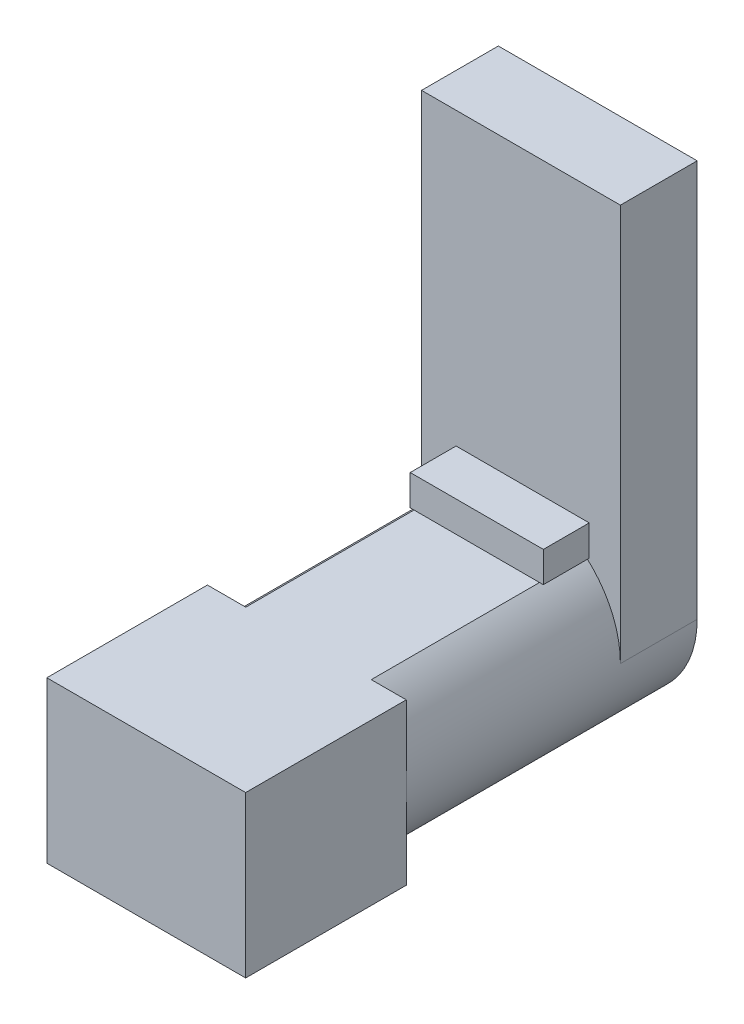
SolidWorks part; units mm, degrees
ref_plane "Front Plane" through (0, 0, 0) normal (0, 0, 1) x (1, 0, 0)
ref_plane "Top Plane" through (0, 0, 0) normal (0, 1, 0) x (1, 0, 0)
ref_plane "Right Plane" through (0, 0, 0) normal (1, 0, 0) x (0, 0, -1)
sketch "Sketch2" plane through (0, 0, 0) normal (0, 0, 1) x (1, 0, 0)
  line L1 (-6.25, -5.3) -> (6.25, -5.3)
  line L2 (-6.25, -5.3) -> (-6.25, 5.3)
  line L3 (-6.25, 5.3) -> (6.25, 5.3)
  line L4 (6.25, -5.3) -> (6.25, 5.3)
  line L5 (-6.25, -5.3) -> (6.25, 5.3) construction
  line L6 (-6.25, 5.3) -> (6.25, -5.3) construction
  line L7 (-6.5, -5.55) -> (6.5, -5.55)
  line L8 (-6.5, -5.55) -> (-6.5, 5.55)
  line L9 (-6.5, 5.55) -> (6.5, 5.55)
  line L10 (6.5, -5.55) -> (6.5, 5.55)
  line L11 (-6.5, -5.55) -> (6.5, 5.55) construction
  line L12 (-6.5, 5.55) -> (6.5, -5.55) construction
  point P0 (0, 0)
  point P6 (0, 0)
  dimension "D1" = 12.5
  dimension "D2" = 10.6
  dimension "D3" = 0.25
  dimension "D4" = 0.25
extrude "Boss-Extrude1" add sketch "Sketch2" along normal blind 10 contours L2 L1 L4 L3 | L8 L7 L10 L9
sketch "Sketch3" plane through (0, 0, 0) normal (0, 0, -1) x (-1, 0, 0)
  line L1 (-6.25, 5.3) -> (6.25, 5.3)
  line L2 (-6.25, 5.3) -> (-6.25, -5.3)
  line L3 (-6.25, -5.3) -> (6.25, -5.3)
  line L4 (6.25, 5.3) -> (6.25, -5.3)
  line L5 (-6.25, 5.3) -> (6.25, -5.3) construction
  line L6 (-6.25, -5.3) -> (6.25, 5.3) construction
  point P0 (0, 0)
extrude "Boss-Extrude2" add sketch "Sketch3" against normal blind 10
sketch "Sketch4" plane through (0, 0, 0) normal (0, 0, -1) x (-1, 0, 0)
  line L0 (-3.3834, -5.55) -> (2.9839, -5.55)
  line L1 (-6.5, 0) -> (6.5, 0) construction
  line L2 (-3.3834, 5.55) -> (2.9839, 5.55)
  line L3 (6.5, 5.55) -> (-6.5, 5.55) construction
  line L4 (-6.5, -5.55) -> (-6.5, 5.55) construction
  line L5 (6.5, -5.55) -> (6.5, 5.55) construction
  arc A0 (-3.3834, -5.55) -> (-3.3834, 5.55) centre (0, 0) cw
  arc A1 (2.9839, -5.55) -> (2.9839, 5.55) centre (0.3617, 0) ccw
  point P15 (-6.5, 0)
  dimension "D1" = 6.1383
extrude "Boss-Extrude3" add sketch "Sketch4" along normal blind 15.5
sketch "Sketch5" plane through (0, 0, -15.5) normal (0, 0, -1) x (-1, 0, 0)
  line L0 (-6.5, 10.96) -> (6.5, 10.96)
  line L1 (-6.5, 10.96) -> (-6.5, 0)
  line L2 (-6.5, 0) -> (6.5, 0)
  line L3 (6.5, 10.96) -> (6.5, 0)
  line L4 (-6.5, 0) -> (-6.5, 5.55) construction
  line L5 (-3.3834, -5.55) -> (2.9839, -5.55)
  arc A0 (-6.5, 0) -> (-3.3834, -5.55) centre (0, 0) ccw
  arc A1 (2.9839, -5.55) -> (6.5, 0) centre (0.3617, 0) ccw
  arc M5 (-3.3834, 5.55) -> (-3.3834, -5.55) centre (0, 0) ccw
  line M6 (-3.3834, -5.55) -> (2.9839, -5.55)
  arc M7 (2.9839, -5.55) -> (2.9839, 5.55) centre (0.3617, 0) ccw
  line M8 (2.9839, 5.55) -> (-3.3834, 5.55)
  dimension "D1" = 10.96
extrude "Boss-Extrude4" add sketch "Sketch5" against normal blind 1.5 contours L2 M5 M6 M7 | L3 L0 L1 M5 M8 M7
sketch "Sketch6" plane through (0, 0, -15.5) normal (0, 0, -1) x (-1, 0, 0)
  line L0 (-6.5, -5.55) -> (-6.5, 0) construction
  line L1 (-6.5, 0) -> (-6.5, 10.96)
  line L2 (-6.5, 10.96) -> (6.5, 10.96)
  line L3 (6.5, 10.96) -> (6.5, 0)
  line L4 (-3.3834, -5.55) -> (2.9839, -5.55)
  arc A0 (-3.3834, -5.55) -> (-6.5, 0) centre (0, 0) cw
  arc A1 (-6.5, 0) -> (-3.3834, -5.55) centre (0, 0) ccw construction
  arc A2 (6.5, 0) -> (2.9839, -5.55) centre (0.3617, 0) cw
extrude "Boss-Extrude5" add sketch "Sketch6" along normal blind 3.52
sketch "Sketch8" plane through (0, 0, -19.02) normal (0, 0, -1) x (-1, 0, 0)
  line L0 (-6.5, 0) -> (6.5, 0) construction
sketch "Sketch9" plane through (0, 0, 10) normal (0, 0, 1) x (1, 0, 0)
  line L1 (-6.5, 5.55) -> (6.5, 5.55)
  line L2 (-6.5, 5.55) -> (-6.5, -5.55)
  line L3 (-6.5, -5.55) -> (6.5, -5.55)
  line L4 (6.5, 5.55) -> (6.5, -5.55)
extrude "Boss-Extrude7" add sketch "Sketch9" along normal blind 0.5
sketch "Sketch10" plane through (-6.5, 0, 0) normal (-1, 0, 0) x (0, 0, 1)
  line L0 (-14, 0) -> (-14, 5.55) construction
  line L1 (10.5, 5.55) -> (-14, 5.55)
  line L2 (10.5, 5.55) -> (10.5, 4.95)
  line L3 (10.5, 4.95) -> (-14, 4.95)
  line L4 (-14, 5.55) -> (-14, 4.95)
  dimension "D1" = 0.6
extrude "Cut-Extrude1" cut sketch "Sketch10" against normal blind 15
sketch "Sketch11" plane through (0, 0, -14) normal (0, 0, 1) x (1, 0, 0)
  line L0 (4.2128, 4.95) -> (-3.9916, 4.95) construction
  line L1 (4.4628, 4.95) -> (-4.2416, 4.95)
  line L2 (0.1106, 4.95) -> (0.1106, 6.95)
  line L3 (4.4628, 6.95) -> (-4.2416, 6.95)
  line L4 (-4.2416, 4.95) -> (-4.2416, 6.95)
  line L5 (4.4628, 4.95) -> (4.4628, 6.95)
  line M6 (-3.9916, 4.95) -> (4.2128, 4.95)
  dimension "D1" = 0.25
  dimension "D2" = 2
extrude "Boss-Extrude8" add sketch "Sketch11" along normal blind 3 contours L4 L1 L2 L3 M6 | L1 L5 L3 L2
sketch "Sketch13" plane through (0, 0, -19.02) normal (0, 0, -1) x (-1, 0, 0)
  line L0 (-0.0481, -5.04) -> (-3.4315, -5.55) construction
  line L1 (-3.4315, -5.55) -> (2.9359, -5.55) construction
  line L2 (-3.3834, -5.55) -> (2.9839, -5.55) construction
  circle A0 centre (-0.0481, -0.29) radius 4.75
  dimension "D1" = 9.5
  dimension "D2" = 0.51
  dimension "D3" = 3.3834
  dimension "D4" = 6.3673
extrude "Boss-Extrude9" add sketch "Sketch13" along normal blind 0.98
sketch "Sketch15" plane through (0, 10.96, 0) normal (0, 1, 0) x (1, 0, 0)
  line L1 (-6.5, 19.02) -> (6.5, 19.02)
  line L2 (-6.5, 19.02) -> (-6.5, 14)
  line L3 (-6.5, 14) -> (6.5, 14)
  line L4 (6.5, 19.02) -> (6.5, 14)
extrude "Boss-Extrude11" add sketch "Sketch15" along normal blind 15
